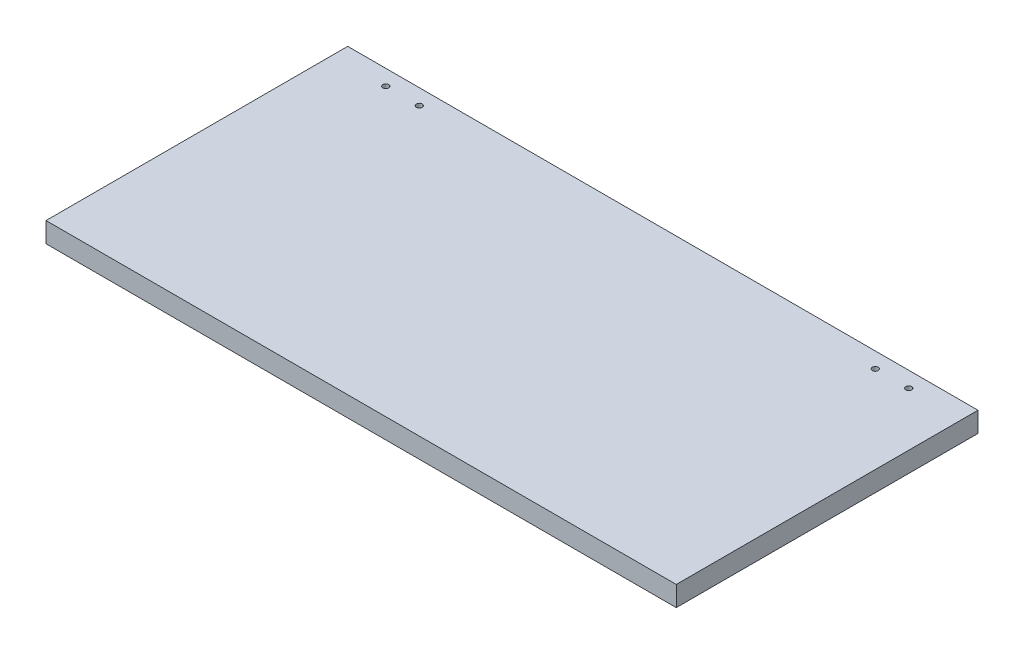
SolidWorks part; units mm, degrees
ref_plane "Front Plane" through (0, 0, 0) normal (0, 0, 1) x (1, 0, 0)
ref_plane "Top Plane" through (0, 0, 0) normal (0, 1, 0) x (1, 0, 0)
ref_plane "Right Plane" through (0, 0, 0) normal (1, 0, 0) x (0, 0, -1)
sketch "Sketch2" plane through (0, 0, 0) normal (0, 1, 0) x (1, 0, 0)
  line L1 (-235, 112.5) -> (235, 112.5)
  line L2 (-235, 112.5) -> (-235, -112.5)
  line L3 (-235, -112.5) -> (235, -112.5)
  line L4 (235, 112.5) -> (235, -112.5)
  line L5 (-235, 112.5) -> (235, -112.5) construction
  line L6 (-235, -112.5) -> (235, 112.5) construction
  point P0 (0, 0)
  dimension "D1" = 470
  dimension "D2" = 225
extrude "Boss-Extrude1" add sketch "Sketch2" along normal blind 15
sketch "Sketch3" plane through (0, 15, 0) normal (0, 1, 0) x (1, 0, 0)
  line L0 (-235, 112.5) -> (-235, -112.5) construction
  line L1 (235, 112.5) -> (-235, 112.5) construction
  line L2 (235, -112.5) -> (235, 112.5) construction
  circle A0 centre (-195, 100.9) radius 2.2
  circle A1 centre (-170, 100.9) radius 2.2
  circle A2 centre (195, 100.9) radius 2.2
  circle A3 centre (170, 100.9099) radius 2.2
  dimension "D1" = 4.4
  dimension "D5" = 4.4
  dimension "D2" = 40
  dimension "D3" = 11.6
  dimension "D6" = 11.6
  dimension "D7" = 40
  dimension "D4" = 2
  dimension "D8" = 2
extrude "Cut-Extrude1" cut sketch "Sketch3" against normal through all
